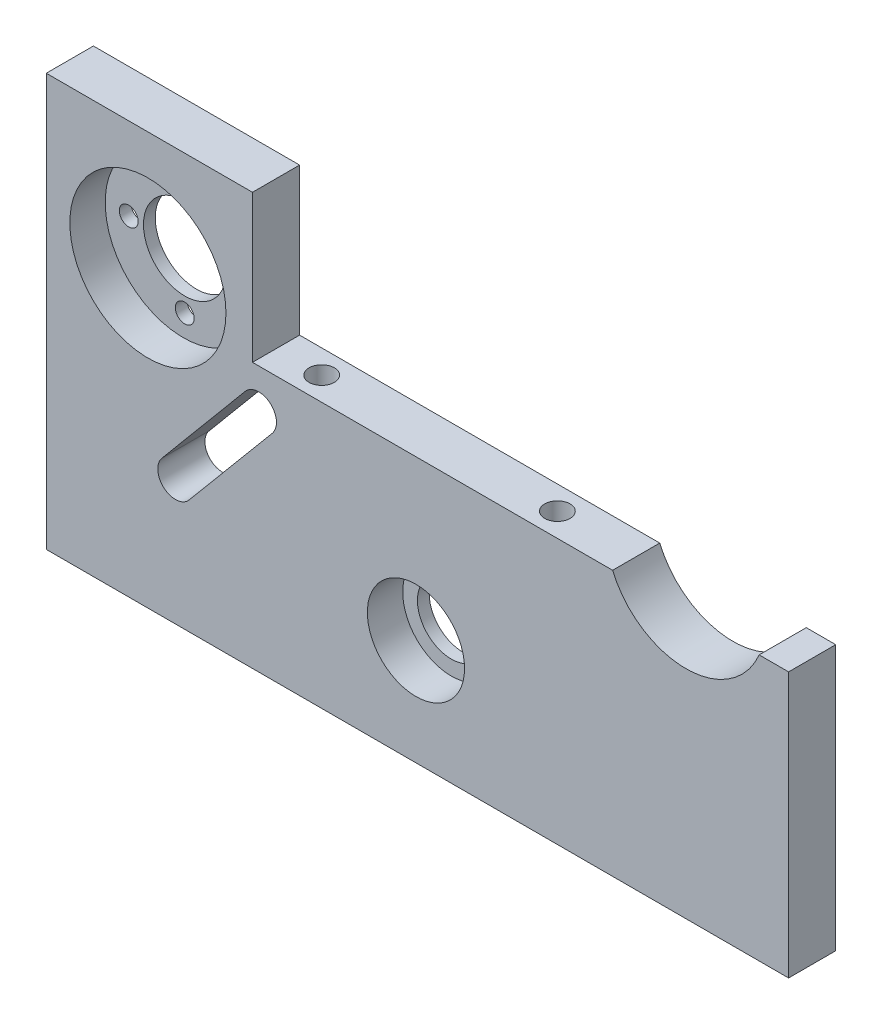
SolidWorks part; units mm, degrees
material "Alliage 1060"
ref_plane "Plan de face" through (0, 0, 0) normal (0, 0, 1) x (1, 0, 0)
ref_plane "Plan de dessus" through (0, 0, 0) normal (0, 1, 0) x (1, 0, 0)
ref_plane "Plan de droite" through (0, 0, 0) normal (1, 0, 0) x (0, 0, -1)
sketch "Esquisse1" plane through (0, 0, 0) normal (0, 0, 1) x (1, 0, 0)
  line L0 (-53.3856, 37.6711) -> (-53.3856, -32.3289)
  line L1 (-53.3856, -32.3289) -> (72.6144, -32.3289)
  line L2 (72.6144, -32.3289) -> (72.6144, 12.6711)
  line L3 (72.6144, 12.6711) -> (-18.3856, 12.6711)
  line L4 (-18.3856, 12.6711) -> (-18.3856, 37.6711)
  line L5 (-18.3856, 37.6711) -> (-53.3856, 37.6711)
  dimension "D1" = 35
  dimension "D2" = 70
  dimension "D3" = 126
  dimension "D4" = 45
extrude "Boss.-Extru.1" add sketch "Esquisse1" along normal blind 8
sketch "Esquisse2" plane through (0, 0, 8) normal (0, 0, 1) x (1, 0, 0)
  line L0 (-18.3856, 37.6711) -> (-53.3856, 37.6711) construction
  line L1 (-49.3856, 17.6711) -> (-53.3856, 17.6711) construction
  line L4 (-53.3856, 37.6711) -> (-53.3856, -32.3289) construction
  circle A0 centre (-36.1356, 17.6711) radius 13.25
  dimension "D1" = 26.5
  dimension "D2" = 20
  dimension "D3" = 4
sketch "Esquisse3" plane through (0, 0, 0) normal (0, 0, -1) x (-1, 0, 0)
  line L0 (35.8856, 30.9187) -> (35.8856, 4.4234) construction
  line L2 (18.3856, 37.6711) -> (53.3856, 37.6711) construction
  line L3 (35.8856, 24.6711) -> (35.8856, 25.6711) construction
  line L4 (53.3856, 37.6711) -> (53.3856, -32.3289) construction
  circle A5 centre (45.3856, 17.6711) radius 1.5
  circle A9 centre (36.1356, 17.6711) radius 13.25 construction
  circle A10 centre (35.8856, 17.6711) radius 7
  circle A11 centre (35.8856, 8.1711) radius 1.5
  circle A12 centre (35.8856, 17.6711) radius 7
  circle A13 centre (26.3856, 17.6711) radius 1.5
  circle A14 centre (35.8856, 17.6711) radius 7
  circle A15 centre (35.8856, 27.1711) radius 1.5
  circle A16 centre (35.8856, 17.6711) radius 7
  point P14 (35.8856, 17.6711)
  point P24 (35.8856, 17.6711)
  dimension "D1" = 17.5
  dimension "D3" = 14
  dimension "D2" = 3
  dimension "D5" = 20
  dimension "D6" = 9.5
  dimension "D4" = 4
sketch "Esquisse4" plane through (0, 0, 8) normal (0, 0, 1) x (1, 0, 0)
  line L0 (72.6144, 12.6711) -> (-18.3856, 12.6711) construction
  line L1 (42.7417, 12.6711) -> (67.6144, 12.6711)
  line L3 (55.1781, 4.4234) -> (55.1781, 21.913) construction
  line L4 (-35.8856, 4.4234) -> (55.1781, 4.4234) construction
  line L5 (-19.6117, 7.7966) -> (-33.76, -9.1029)
  line L6 (-15.0111, 3.945) -> (-29.1595, -12.9545)
  line L10 (72.6144, -32.3289) -> (72.6144, 12.6711) construction
  line L11 (-53.3856, -32.3289) -> (72.6144, -32.3289) construction
  line L14 (-53.3856, 37.6711) -> (-53.3856, -32.3289) construction
  arc A0 (67.6144, 12.6711) -> (42.7417, 12.6711) centre (55.1781, 17.9234) cw
  arc A7 (-19.6117, 7.7966) -> (-15.0111, 3.945) centre (-17.3114, 5.8708) cw
  arc A9 (-33.76, -9.1029) -> (-29.1595, -12.9545) centre (-31.4598, -11.0287) ccw
  point P16 (-33.3856, -13.3289)
  point P21 (-15.3856, 8.1711)
  dimension "D2" = 13.5
  dimension "D4" = 6
  dimension "D1" = 5
  dimension "D5" = 19
  dimension "D6" = 20
  dimension "D7" = 4.5
  dimension "D8" = 88
extrude "Repose moteur" cut sketch "Esquisse4" against normal blind 8
sketch "Esquisse5" plane through (0, 0, 8) normal (0, 0, 1) x (1, 0, 0)
  line L0 (17.6144, -14.3289) -> (72.6144, -14.3289) construction
  line L1 (72.6144, -32.3289) -> (72.6144, 12.6711) construction
  line L4 (-53.3856, -32.3289) -> (72.6144, -32.3289) construction
  line L5 (9.3644, -14.3289) -> (9.3644, 21.228) construction
  circle A0 centre (9.3644, -14.3289) radius 8.25
  dimension "D2" = 16.5
  dimension "D1" = 55
  dimension "D3" = 18
sketch "Esquisse6" plane through (0, 0, 0) normal (0, 0, -1) x (-1, 0, 0)
  circle A0 centre (-9.3644, -14.3289) radius 5.75
  dimension "D1" = 11.5
extrude "Fixation courroi 1" cut sketch "Esquisse5" against normal blind 6
extrude "Fixation courroi 2" cut sketch "Esquisse6" against normal blind 2
extrude "Fixation moteur 1" cut sketch "Esquisse3" against normal blind 2 contours L0 A10 | A16 L0
extrude "Fixation moteur 2" cut sketch "Esquisse2" against normal blind 6
sketch "Esquisse7" plane through (0, -32.3289, 0) normal (0, -1, 0) x (1, 0, 0)
  line L0 (-53.3856, 8) -> (-53.3856, 0) construction
  line L1 (72.6144, 8) -> (72.6144, 0) construction
  circle A0 centre (-49.3856, 3.8003) radius 1.75
  circle A1 centre (-14.3856, 3.8003) radius 1.75
  circle A2 centre (37.6144, 3.8003) radius 1.75
  circle A3 centre (68.6144, 3.8003) radius 1.75
  dimension "D5" = 3.5
  dimension "D6" = 3.5
  dimension "D7" = 3.5
  dimension "D8" = 3.5
  dimension "D1" = 4
  dimension "D2" = 35
  dimension "D3" = 4
  dimension "D4" = 35
sketch "Esquisse9" plane through (0, 12.6711, 0) normal (0, 1, 0) x (1, 0, 0)
  line L0 (9.3644, -8) -> (9.3644, 0) construction
  line L1 (1.1144, -8) -> (17.6144, -8) construction
  line L2 (42.7417, 0) -> (-18.3856, 0) construction
  line L3 (9.3644, -4) -> (-10.6356, -4) construction
  line L4 (9.3644, -4) -> (29.3644, -4) construction
  circle A0 centre (-10.6356, -4) radius 1.75
  circle A1 centre (29.3644, -4) radius 1.75
  dimension "D1" = 3.5
  dimension "D2" = 3.5
  dimension "D3" = 40
hole_wizard "Dégagement M31" positions "Esquisse3D1" profile "Esquisse10" hole size "M3" standard "ISO"
sketch3d "Esquisse3D1"
  point P0 (-26.3856, 17.6711, 0)
  point P3 (-35.8856, 27.1711, 0)
  point P6 (-45.3856, 17.6711, 0)
  point P9 (-35.8856, 8.1711, 0)
sketch "Esquisse10" plane through (-26.3856, 17.6711, 0) normal (1, 0, 0) x (0, 1, 0)
  line L0 (0, 0) -> (0, 10.9614)
  line L1 (0, 10.9614) -> (1.6, 10)
  line L2 (1.6, 10) -> (1.6, 0)
  line L5 (1.6, 0) -> (0, 0)
  line L10 (0, 10.9614) -> (-1.6, 10) construction
  line L11 (0, -6.35) -> (0, 107.95) construction
  dimension "Diamètre du perçage" = 3.2
  dimension "Profondeur du perçage" = 10
  dimension "Angle de pointe" = 118
hole_wizard "Dégagement M41" positions "Esquisse3D2" profile "Esquisse11" hole size "M4" standard "ISO"
sketch3d "Esquisse3D2"
  point P0 (-10.6356, 12.6711, 4)
  point P3 (29.3644, 12.6711, 4)
sketch "Esquisse11" plane through (-10.6356, 12.6711, 4) normal (1, 0, 0) x (0, 0, 1)
  line L0 (0, 0) -> (0, 11.2919)
  line L1 (0, 11.2919) -> (2.15, 10)
  line L2 (2.15, 10) -> (2.15, 0)
  line L5 (2.15, 0) -> (0, 0)
  line L10 (0, 11.2919) -> (-2.15, 10) construction
  line L11 (0, -6.35) -> (0, 107.95) construction
  dimension "Diamètre du perçage" = 4.3
  dimension "Profondeur du perçage" = 10
  dimension "Angle de pointe" = 118
extrude "Enlèv. mat.-Extru.1" cut sketch "Esquisse7" against normal blind 10
